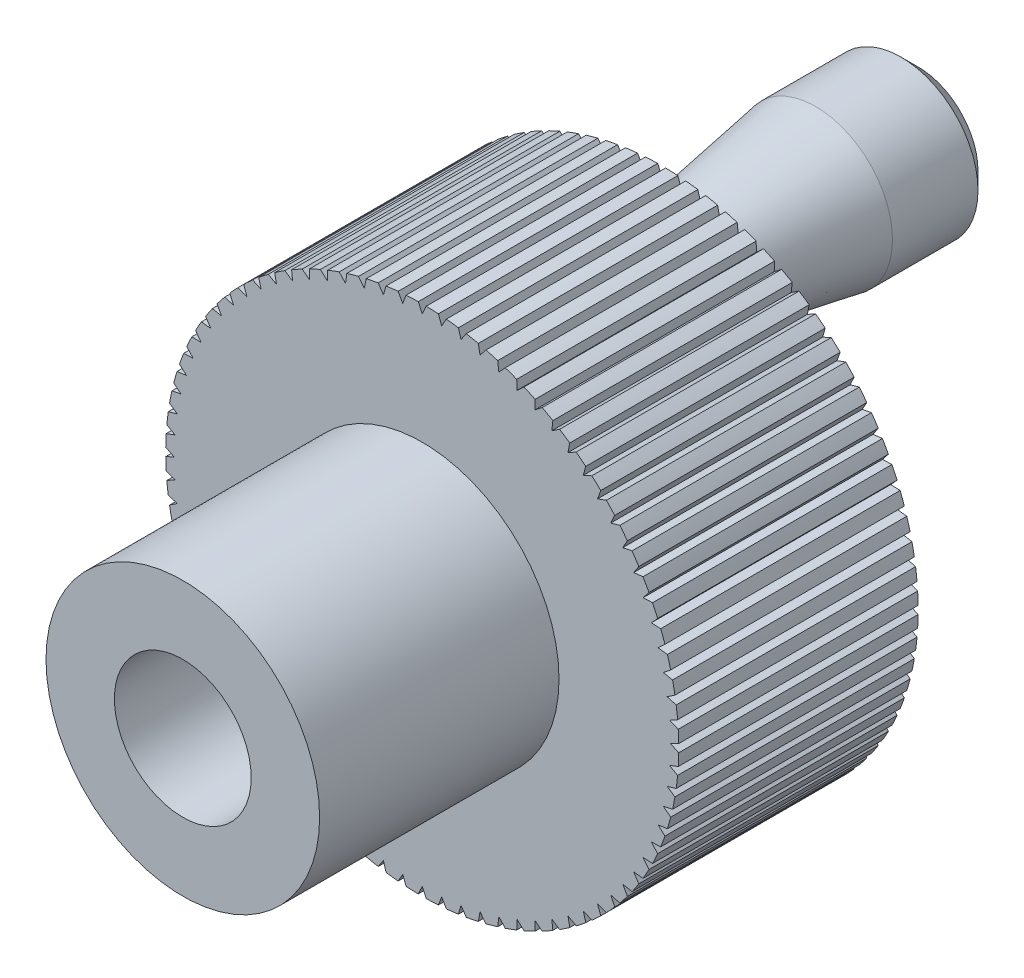
SolidWorks part; units mm, degrees
ref_plane "前视基准面" through (0, 0, 0) normal (0, 0, 1) x (1, 0, 0)
ref_plane "上视基准面" through (0, 0, 0) normal (0, 1, 0) x (1, 0, 0)
ref_plane "右视基准面" through (0, 0, 0) normal (1, 0, 0) x (0, 0, -1)
sketch "草图1" plane through (0, 0, 0) normal (0, 0, 1) x (1, 0, 0)
  circle A0 centre (0, 0) radius 4
  circle A1 centre (0, 0) radius 8
  point P5 (0.3209, 0)
  dimension "D1" = 8
  dimension "D2" = 16
extrude "凸台-拉伸1" add sketch "草图1" along normal blind 14
sketch "草图2" plane through (0, 0, 0) normal (0, 0, -1) x (-1, 0, 0)
  circle A0 centre (0, 0) radius 15
  dimension "D1" = 30
extrude "凸台-拉伸2" add sketch "草图2" along normal blind 14
sketch "草图4" plane through (0, 0, 0) normal (1, 0, 0) x (0, 0, -1)
  line L0 (14, 9) -> (29, 9)
  line L1 (14, -15) -> (14, 15) construction
  line L2 (29, 9) -> (29, 13.5)
  line L3 (29, 13.5) -> (23, 13.5)
  line L4 (23, 13.5) -> (14, 12)
  line L5 (14, 12) -> (14, 9)
  point P5 (21.3619, 14.2537)
  dimension "D1" = 15
  dimension "D2" = 9
  dimension "D3" = 4.5
  dimension "D4" = 6
  dimension "D5" = 3
revolve "旋转1" add sketch "草图4" angle 360 about L0
chamfer "倒角1" distance 1 angle 45 1 edges at (4.5, 9, -29)
sketch "草图5" plane through (0, 0, -14) normal (0, 0, -1) x (-1, 0, 0)
  line L0 (-15, 0) -> (-14.5, 0) construction
  line L1 (-14.5, 0) -> (-14.9982, 0.2323)
  line L2 (-14.5, 0) -> (-14.9982, -0.2323)
  circle A0 centre (0, 0) radius 15 construction
  arc A1 (-14.9982, 0.2323) -> (-14.9982, -0.2323) centre (0, 0) ccw
  point P6 (-15, 0.8191)
  dimension "D1" = 50
  dimension "D2" = 0.5
extrude "切除-拉伸1" cut sketch "草图5" against normal through all
pattern_circular "阵列(圆周)1" count 80 over 360 about axis through (0, 0, 0) along (0, 0, 1) of "切除-拉伸1"
